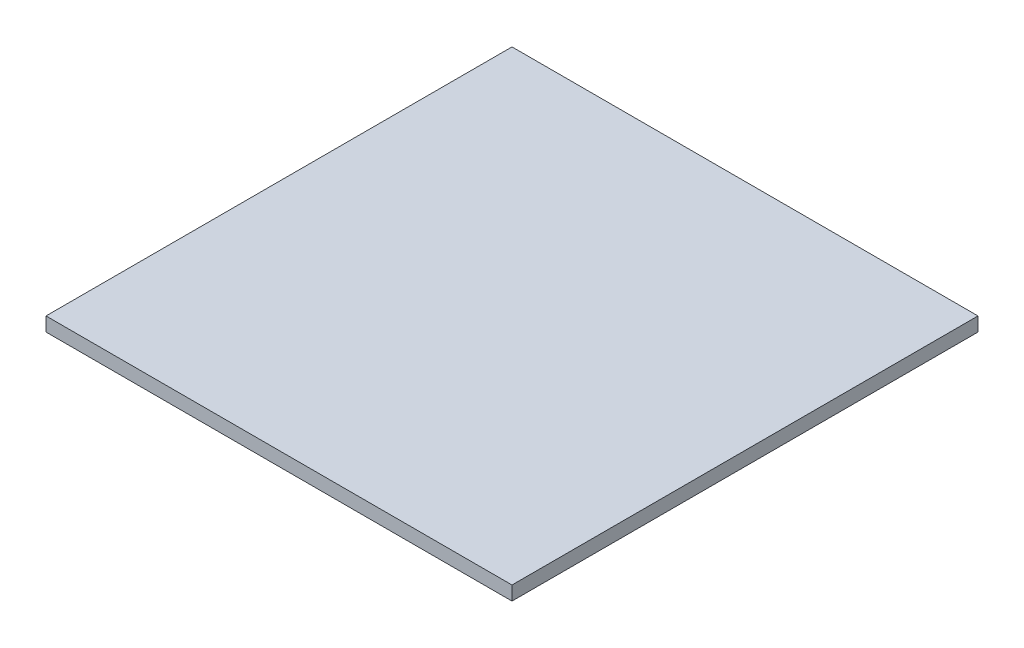
SolidWorks part; units mm, degrees
ref_plane "Front Plane" through (0, 0, 0) normal (0, 0, 1) x (1, 0, 0)
ref_plane "Top Plane" through (0, 0, 0) normal (0, 1, 0) x (1, 0, 0)
ref_plane "Right Plane" through (0, 0, 0) normal (1, 0, 0) x (0, 0, -1)
sketch "Sketch1" plane through (0, 0, 0) normal (0, 1, 0) x (1, 0, 0)
  line L1 (50, -50) -> (-50, -50)
  line L2 (50, -50) -> (50, 50)
  line L3 (50, 50) -> (-50, 50)
  line L4 (-50, -50) -> (-50, 50)
  line L5 (50, -50) -> (-50, 50) construction
  line L6 (50, 50) -> (-50, -50) construction
  point P0 (0, 0)
  dimension "D1" = 100
  dimension "D2" = 100
extrude "Boss-Extrude1" add sketch "Sketch1" along normal blind 3
sketch "Sketch2" plane through (0, 3, 0) normal (0, 1, 0) x (1, 0, 0)
  line L0 (-50, -50) -> (50, -50) construction
  line L1 (-50, 50) -> (-50, -50) construction
  line L2 (-25, 8.3) -> (-25, -40) construction
  line L3 (-23.4, 8.3) -> (-25, 8.3) construction
  line L4 (27.4, -7) -> (27.4, -34.9) construction
  circle A0 centre (-23.4, 8.3) radius 1.6
  circle A1 centre (27.4, -7) radius 1.6
  circle A2 centre (27.4, -34.9) radius 1.6
  circle A3 centre (-25, -40) radius 1.6
  dimension "D1" = 3.2
  dimension "D2" = 48.3
  dimension "D3" = 5.1
  dimension "D4" = 10
  dimension "D5" = 25
  dimension "D8" = 27.9
  dimension "D9" = 50.8
extrude "Cut-Extrude1" [suppressed] cut sketch "Sketch2" against normal through all
